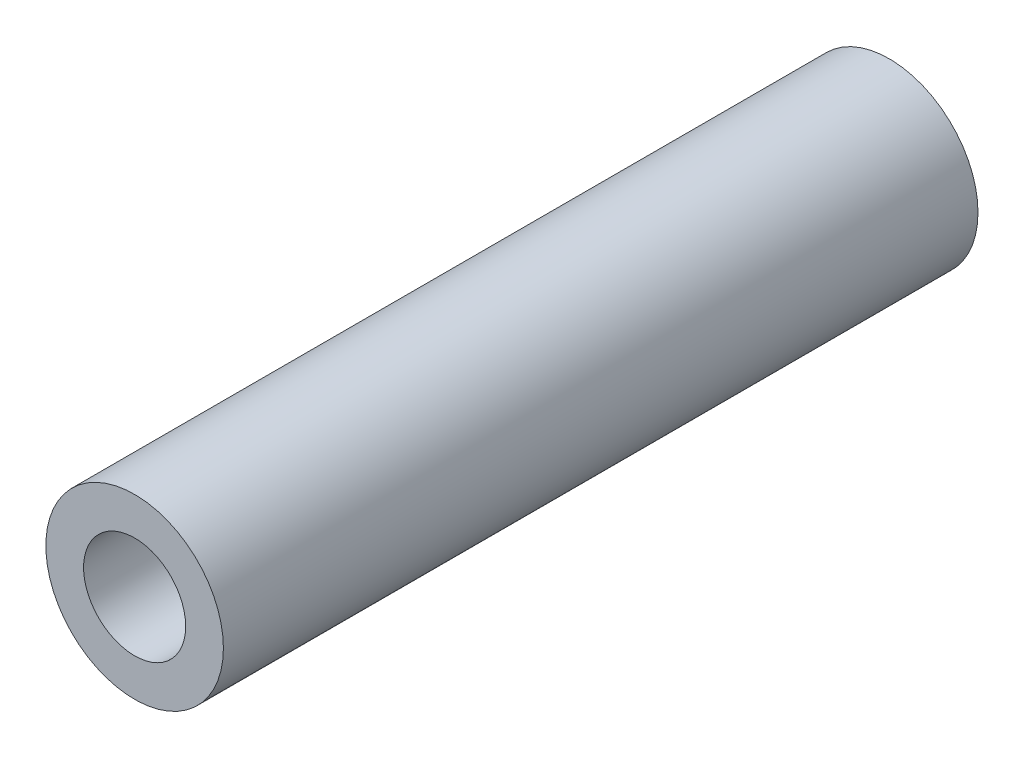
SolidWorks part; units mm, degrees
material "POM copolymère d'acétal"
ref_plane "Plan de face" through (0, 0, 0) normal (0, 0, 1) x (1, 0, 0)
ref_plane "Plan de dessus" through (0, 0, 0) normal (0, 1, 0) x (1, 0, 0)
ref_plane "Plan de droite" through (0, 0, 0) normal (1, 0, 0) x (0, 0, -1)
sketch "Esquisse1" plane through (0, 0, 0) normal (0, 0, 1) x (1, 0, 0)
  circle A0 centre (0, 0) radius 2.3
  circle A1 centre (0, 0) radius 4
  dimension "D1" = 4.6
  dimension "D2" = 8
extrude "Boss.-Extru.1" add sketch "Esquisse1" along normal mid plane 34
